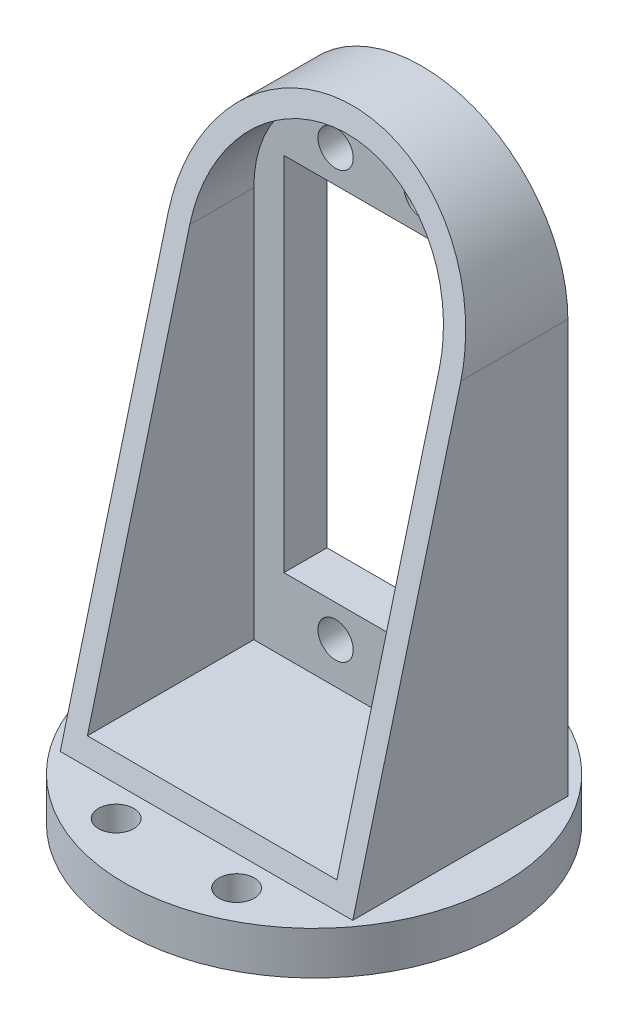
SolidWorks part; units mm, degrees
ref_plane "Front" through (0, 0, 0) normal (0, 0, 1) x (1, 0, 0)
ref_plane "Top" through (0, 0, 0) normal (0, 1, 0) x (1, 0, 0)
ref_plane "Right" through (0, 0, 0) normal (1, 0, 0) x (0, 0, -1)
sketch "Sketch1" plane through (0, 0, 0) normal (0, 0, 1) x (1, 0, 0)
  line L0 (-17, 16) -> (-17, -32)
  line L1 (-11, -21) -> (11, -21)
  line L2 (-11, -21) -> (-11, 21)
  line L3 (-11, 21) -> (11, 21)
  line L4 (11, -21) -> (11, 21)
  line L5 (-11, -21) -> (11, 21) construction
  line L6 (-11, 21) -> (11, -21) construction
  line L7 (-10, -27.25) -> (10, -27.25) construction
  line L8 (-10, -27.25) -> (-10, 27.25) construction
  line L9 (-10, 27.25) -> (10, 27.25) construction
  line L10 (10, -27.25) -> (10, 27.25) construction
  line L11 (-10, -27.25) -> (10, 27.25) construction
  line L12 (-10, 27.25) -> (10, -27.25) construction
  line L13 (17, 16) -> (17, -32)
  line L14 (17, -32) -> (-17, -32)
  circle A0 centre (0, 16) radius 17
  circle A1 centre (-5, 24.75) radius 2.05
  circle A2 centre (5, 24.75) radius 2.05
  circle A3 centre (-5, -24.75) radius 2.05
  circle A4 centre (5, -24.75) radius 2.05
  circle A5 centre (0, 10) radius 6
  point P0 (0, 0)
  point P5 (0, 0)
  dimension "D5" = 34
  dimension "D8" = 4.1
  dimension "D9" = 4.1
  dimension "D15" = 12
  dimension "D1" = 42
  dimension "D2" = 22
  dimension "D3" = 54.5
  dimension "D4" = 20
  dimension "D6" = 16
  dimension "D7" = 32
  dimension "D10" = 5
  dimension "D11" = 10
  dimension "D12" = 3.75
  dimension "D14" = 49.5
  dimension "D16" = 10
  dimension "D13" = 2
extrude "Boss-Extrude1" add sketch "Sketch1" along normal blind 5 contours A0 L8 L9 L10 | L8 A0 L10 L9 A5 A2 A1 | A0 L0 L14 L13 L10 L7 L8 | A0 L8 L7 L10 A4 A3 | L2 L1 L4 L3
sketch "Sketch2" plane through (0, 0, 5) normal (0, 0, 1) x (1, 0, 0)
  line L0 (-14.5, 16) -> (-14.5, -29.5)
  line L1 (-14.5, -29.5) -> (14.5, -29.5)
  line L2 (14.5, -29.5) -> (14.5, 16)
  line L3 (17, -32) -> (17, 16)
  line L4 (-17, 16) -> (-17, -32)
  line L5 (-17, -32) -> (17, -32)
  line L6 (17, -32) -> (17, 16)
  line L7 (-17, 16) -> (-17, -32)
  line L8 (-17, -32) -> (17, -32)
  arc A0 (14.5, 16) -> (-14.5, 16) centre (0, 16) ccw
  arc A1 (17, 16) -> (-17, 16) centre (0, 16) ccw
  arc A2 (17, 16) -> (-17, 16) centre (0, 16) ccw
  dimension "D1" = 0
  dimension "D2" = 2.5
extrude "Boss-Extrude2" add sketch "Sketch2" along normal blind 20
sketch "Sketch3" plane through (17, 0, 0) normal (1, 0, 0) x (0, 0, -1)
  line L0 (-25, -32) -> (-8, 33)
  line L1 (0, 33) -> (-25, 33) construction
  line L2 (-8, 33) -> (-25, 33)
  line L3 (-25, 33) -> (-25, -32)
  line L4 (0, 16) -> (0, 33) construction
  dimension "D1" = 8
extrude "Cut-Extrude1" cut sketch "Sketch3" against normal through all
sketch "Sketch4" plane through (0, -32, 0) normal (0, -1, 0) x (1, 0, 0)
  line L0 (0, 0) -> (0, 25) construction
  line L1 (-17, 25) -> (17, 25) construction
  circle A0 centre (0, 12.5) radius 22
  dimension "D1" = 44
extrude "Boss-Extrude3" add sketch "Sketch4" along normal blind 5
sketch "Sketch5" plane through (0, -32, 0) normal (0, 1, 0) x (1, 0, 0)
  circle A0 centre (0, 5) radius 2.05
  circle A1 centre (0, -12.5) radius 22 construction
  circle A2 centre (-7, -28.5) radius 2.05
  circle A3 centre (7, -28.5) radius 2.05
  dimension "D1" = 4.1
  dimension "D3" = 4.1
  dimension "D4" = 4.1
  dimension "D2" = 17.5
  dimension "D5" = 7
  dimension "D6" = 7
  dimension "D7" = 16
extrude "Cut-Extrude2" cut sketch "Sketch5" against normal blind 5
